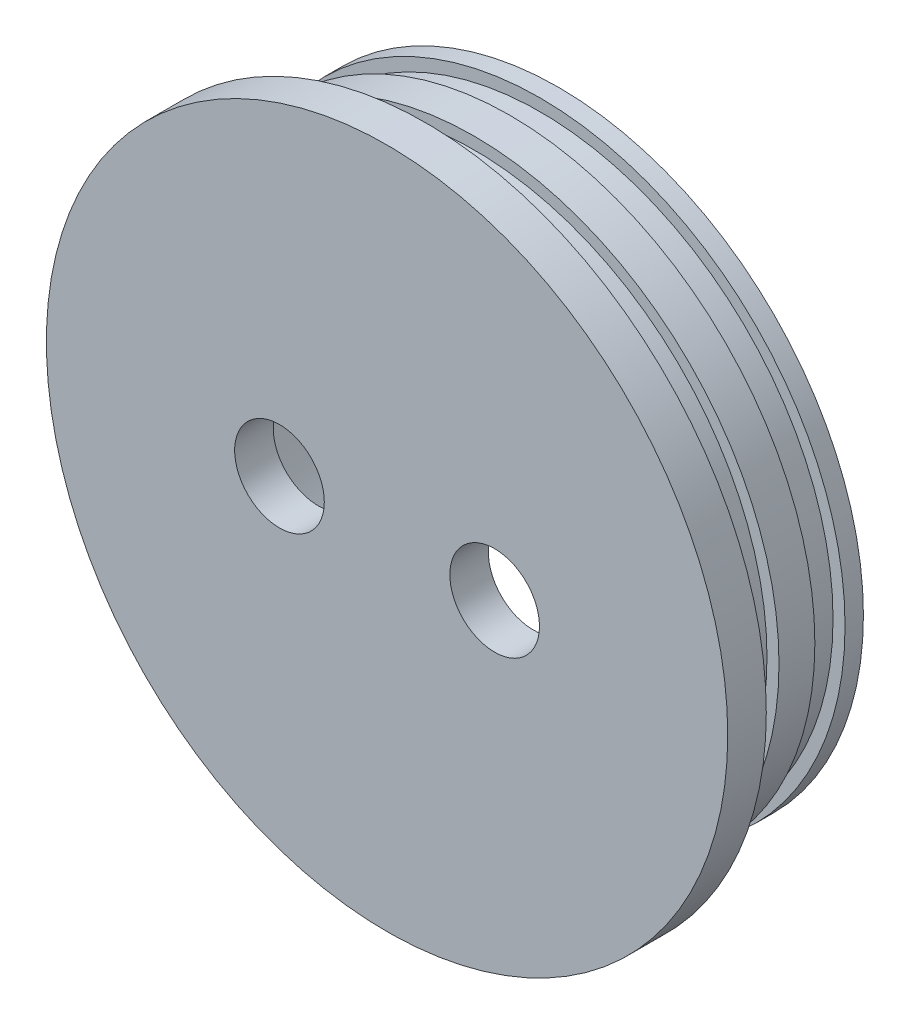
SolidWorks part; units mm, degrees
ref_plane "Front Plane" through (0, 0, 0) normal (0, 0, 1) x (1, 0, 0)
ref_plane "Top Plane" through (0, 0, 0) normal (0, 1, 0) x (1, 0, 0)
ref_plane "Right Plane" through (0, 0, 0) normal (1, 0, 0) x (0, 0, -1)
sketch "Sketch1" plane through (0, 0, 0) normal (1, 0, 0) x (0, 0, -1)
  line L0 (-6.45, 6) -> (0, 6)
  line L1 (0, 6) -> (0, 0)
  line L2 (0, 0) -> (3.075, 0)
  line L3 (22.25, 0) -> (22.25, -7.6)
  line L4 (22.25, -7.6) -> (0, -7.6)
  line L5 (0, -7.6) -> (0, -51)
  line L6 (0, -51) -> (-6.45, -51)
  line L7 (-6.45, -51) -> (-6.45, 6)
  line L8 (8.125, 0) -> (14.125, 0)
  line L10 (3.075, 0) -> (3.075, -2.0094)
  line L11 (3.075, -2.0094) -> (8.125, -2.0094)
  line L12 (8.125, 0) -> (8.125, -2.0094)
  line L14 (14.125, 0) -> (14.125, -2.0094)
  line L15 (14.125, -2.0094) -> (19.175, -2.0094)
  line L16 (19.175, 0) -> (19.175, -2.0094)
  line L17 (19.175, 0) -> (22.25, 0)
  line L18 (-6.45, -51) -> (44.9262, -51) construction
  dimension "D1" = 57
  dimension "D2" = 6.45
  dimension "D3" = 22.25
  dimension "D4" = 6
  dimension "D5" = 7.6
  dimension "D6" = 5.05
  dimension "D7" = 5.05
revolve "Revolve1" add sketch "Sketch1" angle 360 about L18
sketch "Sketch2" plane through (0, 0, 6.45) normal (0, 0, 1) x (1, 0, 0)
  line L0 (0, 6) -> (0, -108) construction
  line L1 (57, -51) -> (-57, -51) construction
  circle A0 centre (0, -51) radius 57 construction
  circle A1 centre (18, -51) radius 7.5
  circle A2 centre (-18, -51) radius 7.5
  point P11 (0, -51)
  dimension "D1" = 15
  dimension "D2" = 15
  dimension "D3" = 18
  dimension "D4" = 18
extrude "Cut-Extrude2" cut sketch "Sketch2" against normal through all
